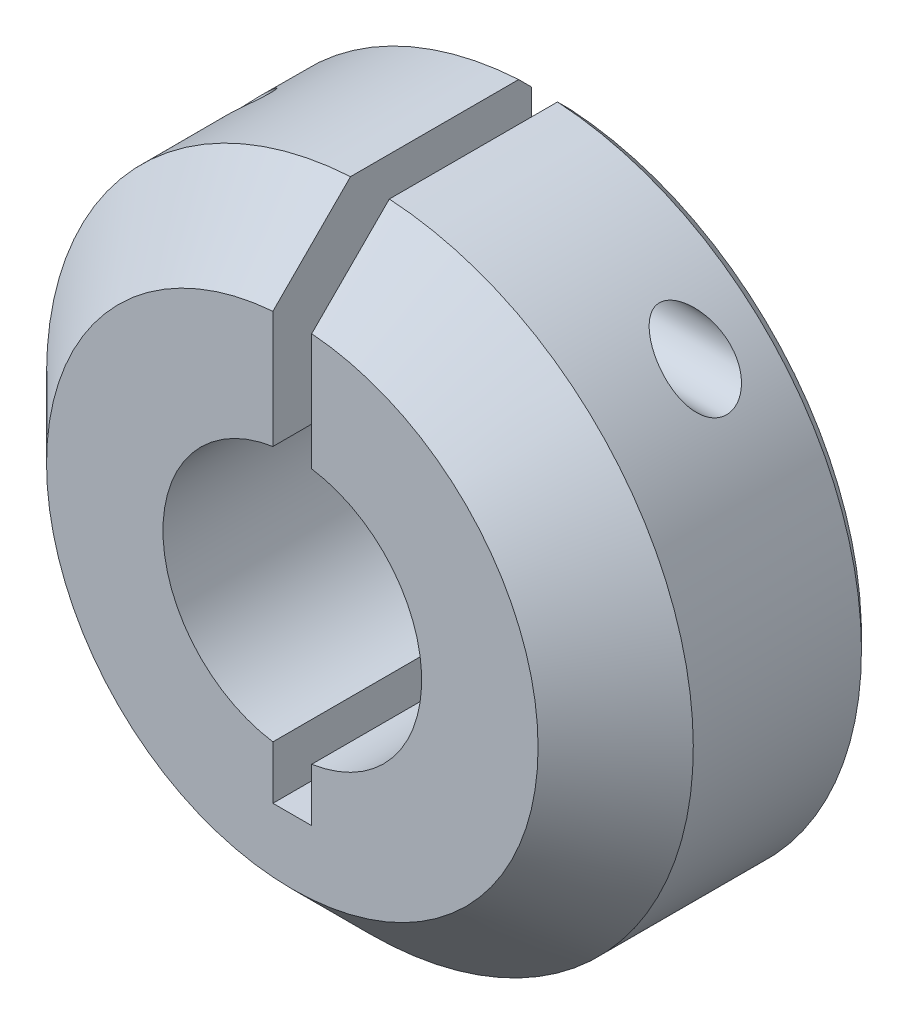
SolidWorks part; units mm, degrees
ref_plane "Front Plane" through (0, 0, 0) normal (0, 0, 1) x (1, 0, 0)
ref_plane "Top Plane" through (0, 0, 0) normal (0, 1, 0) x (1, 0, 0)
ref_plane "Right Plane" through (0, 0, 0) normal (1, 0, 0) x (0, 0, -1)
sketch "Sketch1" plane through (0, 0, 0) normal (0, 0, 1) x (1, 0, 0)
  line L0 (-0.75, 4.9434) -> (-0.75, 12.4775)
  line L1 (0.75, 4.9434) -> (0.75, 12.4775)
  line L2 (-0.75, -4.9434) -> (-0.75, -7)
  line L3 (-0.75, -7) -> (0.75, -7)
  line L4 (0.75, -4.9434) -> (0.75, -7)
  arc A0 (-0.75, 12.4775) -> (0.75, 12.4775) centre (0, 0) ccw
  arc A1 (0.75, -4.9434) -> (0.75, 4.9434) centre (0, 0) ccw
  arc A2 (-0.75, 4.9434) -> (-0.75, -4.9434) centre (0, 0) ccw
  dimension "D1" = 25
  dimension "D2" = 10
  dimension "D4" = 0.75
extrude "Boss-Extrude1" add sketch "Sketch1" along normal blind 10
chamfer "Chamfer1" distance 3 angle 45 1 edges at (0, -12.5, 10)
chamfer "Chamfer2" distance 0.5 angle 45 1 edges at (0, -12.5, 0)
ref_plane "Plane1" through (14.25, 0, 0) normal (1, 0, 0) x (0, 0, -1)
sketch "Sketch22" plane through (14.25, 0, 0) normal (1, 0, 0) x (0, 0, -1)
  line L1 (0, -12) -> (0, 11.9765) construction
  circle A0 centre (-3, 9) radius 1.225
  point P5 (0, 8.1916)
  dimension "D1" = 9
  dimension "D3" = 2.45
  dimension "D2" = 3
extrude "Cut-Extrude1" cut sketch "Sketch22" against normal blind 10
sketch "Sketch23" plane through (14.25, 0, 0) normal (1, 0, 0) x (0, 0, -1)
  circle A0 centre (-3, 9) radius 0.725
  dimension "D1" = 1.45
extrude "Cut-Extrude2" cut sketch "Sketch23" against normal through all
